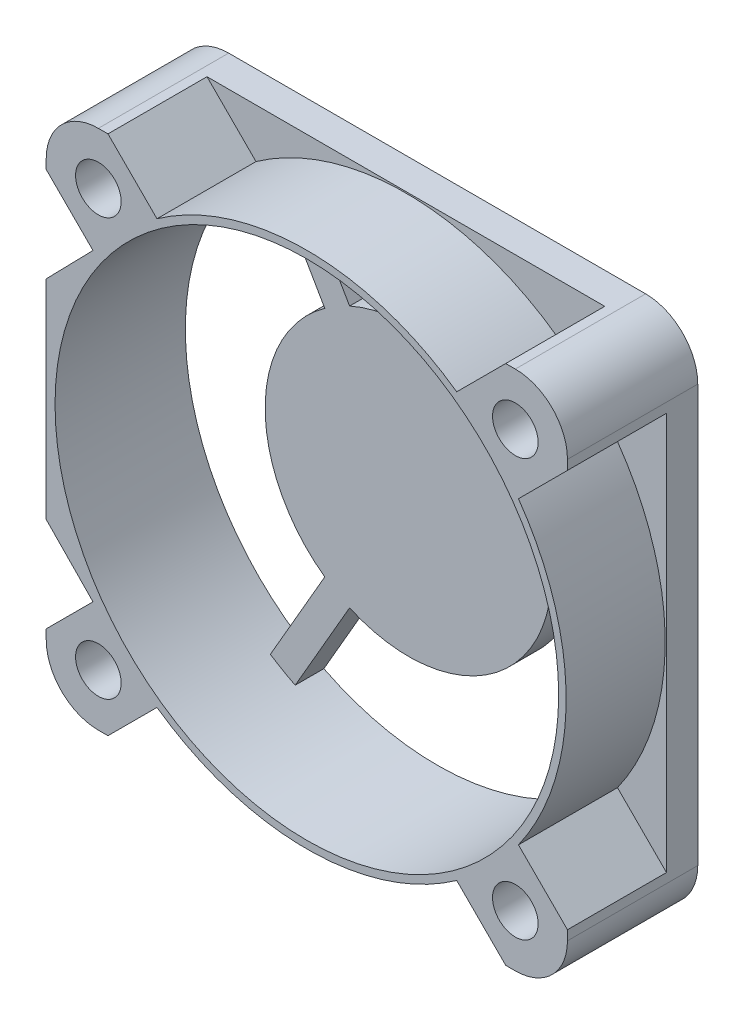
SolidWorks part; units mm, degrees
ref_plane "Front" through (0, 0, 0) normal (0, 0, 1) x (1, 0, 0)
ref_plane "Top" through (0, 0, 0) normal (0, 1, 0) x (1, 0, 0)
ref_plane "Right" through (0, 0, 0) normal (1, 0, 0) x (0, 0, -1)
sketch "Sketch21" plane through (0, 0, 0) normal (0, 0, 1) x (1, 0, 0)
  line L0 (20, 20) -> (-20, 20)
  line L1 (-20, 20) -> (-20, -20)
  line L2 (-20, -20) -> (20, -20)
  line L3 (20, -20) -> (20, 20)
  line L4 (-20, -20) -> (20, 20) construction
  line L5 (-20, 20) -> (20, -20) construction
  dimension "D1" = 40
extrude "Boss-Extrude4" add sketch "Sketch21" along normal mid plane 10 separate body
fillet "Fillet3" radius 4 4 edges at (-20, -20, 0) (20, 20, 0) (20, -20, 0) (-20, 20, 0)
sketch "Sketch22" plane through (0, 0, 5) normal (0, 0, 1) x (1, 0, 0)
  circle A0 centre (0, 0) radius 19.325
  dimension "D1" = 38.65
extrude "Cut-Extrude11" cut sketch "Sketch22" against normal through all
sketch "Sketch23" plane through (0, 0, 5) normal (0, 0, 1) x (1, 0, 0)
  line L0 (16, 20) -> (-16, 20) construction
  line L1 (0, 0) -> (-11.3307, 11.3307) construction
  line L2 (15.2624, 20) -> (11.5018, 16.2394)
  line L6 (-15.2624, 20) -> (-11.5018, 16.2394)
  line L7 (15.2624, 20) -> (-15.2624, 20)
  line L16 (0, 22.353) -> (0, 0) construction
  line L17 (0, 0) -> (13.1623, 0) construction
  circle A0 centre (0, 0) radius 19.325 construction
  arc A3 (-11.5018, 16.2394) -> (11.5018, 16.2394) centre (0, 0) cw
  dimension "D1" = 19.9
  dimension "D2" = 45
  dimension "D3" = 6.7
extrude "Cut-Extrude12" cut sketch "Sketch23" against normal blind 7.6
sketch "Sketch30" plane through (0, 0, 5) normal (0, 0, 1) x (1, 0, 0)
  circle A0 centre (-16, 16) radius 1.75
  arc A1 (-16, 20) -> (-20, 16) centre (-16, 16) ccw construction
  dimension "D1" = 3.5
extrude "Cut-Extrude13" cut sketch "Sketch30" against normal up to next (10 mm away)
pattern_circular "CirPattern2" count 4 over 360 about axis through (0, 0, 0) along (0, 0, 1) of "Cut-Extrude13", "Cut-Extrude12"
sketch "Sketch20" plane through (0, 0, -5) normal (0, 0, -1) x (-1, 0, 0)
  line L0 (6.4251, 8.9285) -> (10.5995, 16.1588)
  line L1 (-10.9449, 1.1) -> (-19.2937, 1.1)
  line L2 (-19.2937, -1.1) -> (-10.9449, -1.1)
  line L3 (8.6942, -17.2588) -> (4.5198, -10.0285)
  line L4 (6.4251, -8.9285) -> (10.5995, -16.1588)
  line L5 (8.6942, 17.2588) -> (4.5198, 10.0285)
  line L6 (0, 0) -> (-8.108, 0) construction
  line L7 (9.6625, 16.7359) -> (0, 0) construction
  arc A0 (10.5995, 16.1588) -> (8.6942, 17.2588) centre (0, 0) ccw
  arc A1 (4.5198, 10.0285) -> (-10.9449, 1.1) centre (0, 0) ccw
  arc A2 (-19.2937, 1.1) -> (-19.2937, -1.1) centre (0, 0) ccw
  arc A3 (-10.9449, -1.1) -> (4.5198, -10.0285) centre (0, 0) ccw
  arc A4 (10.5995, -16.1588) -> (8.6942, -17.2588) centre (0, 0) cw
  arc A5 (6.4251, -8.9285) -> (6.4251, 8.9285) centre (0, 0) ccw
  circle A6 centre (0, 0) radius 19.325 construction
  dimension "D1" = 11
  dimension "D2" = 2.2
  dimension "D3" = 120
extrude "Boss-Extrude3" add sketch "Sketch20" against normal blind 2.2
sketch "Sketch31" plane through (0, 0, 5) normal (0, 0, 1) x (1, 0, 0)
  line L0 (-14.2403, 13.9005) -> (-20, 8)
  line L1 (-20, 15.2624) -> (-20, -15.2624) construction
  line L2 (-20, 8) -> (-20, -8)
  line L3 (-20, -8) -> (-14.2403, -13.9005)
  line L4 (0, 0) -> (-20, 0) construction
  arc A0 (-16.2394, 11.5018) -> (-16.2394, -11.5018) centre (0, 0) ccw construction
  arc A1 (-16.2394, 11.5018) -> (-16.2394, -11.5018) centre (0, 0) ccw construction
  arc A2 (-14.2403, 13.9005) -> (-14.2403, -13.9005) centre (0, 0) ccw
  dimension "D1" = 16
extrude "Boss-Extrude5" add sketch "Sketch31" against normal up to body
